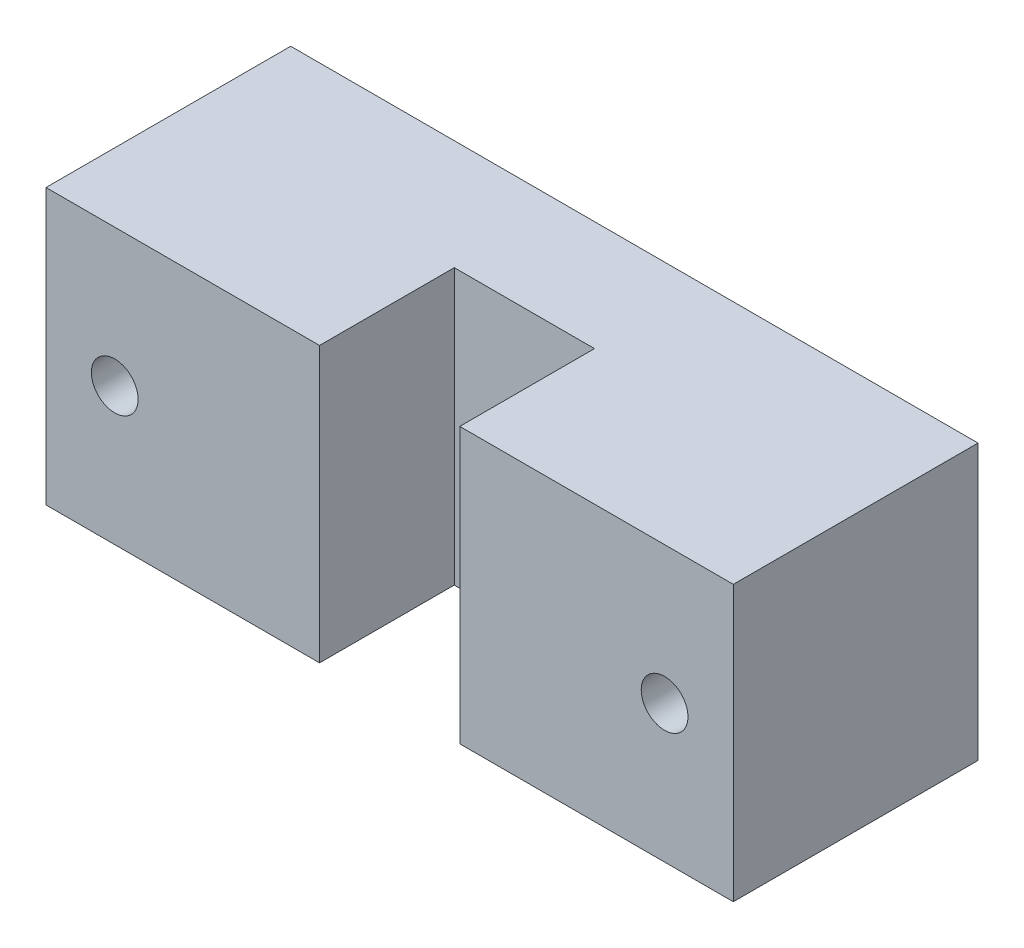
SolidWorks part; units mm, degrees
ref_plane "Спереди" through (0, 0, 0) normal (0, 0, 1) x (1, 0, 0)
ref_plane "Сверху" through (0, 0, 0) normal (0, 1, 0) x (1, 0, 0)
ref_plane "Справа" through (0, 0, 0) normal (1, 0, 0) x (0, 0, -1)
sketch "Sketch2" plane through (0, 0, 0) normal (0, 0, 1) x (1, 0, 0)
  line L0 (20, 0) -> (-20, 0) construction
  line L1 (25, -10) -> (-25, -10)
  line L2 (25, -10) -> (25, 10)
  line L3 (25, 10) -> (-25, 10)
  line L4 (-25, -10) -> (-25, 10)
  line L5 (25, -10) -> (-25, 10) construction
  line L6 (25, 10) -> (-25, -10) construction
  circle A0 centre (-20, 0) radius 1.7
  circle A1 centre (20, 0) radius 1.7
  point P0 (0, 0)
  point P9 (0, 0)
  dimension "D4" = 3.4
  dimension "D1" = 20
  dimension "D2" = 50
  dimension "D3" = 40
extrude "Boss-Extrude1" add sketch "Sketch2" along normal blind 8
sketch "Sketch5" plane through (0, -10, 0) normal (0, -1, 0) x (1, 0, 0)
  line L0 (-25, 8) -> (-25, 17.8)
  line L1 (-25, 8) -> (25, 8) construction
  line L2 (-25, 17.8) -> (-5.1, 17.8)
  line L3 (-5.1, 17.8) -> (-5.1, 8)
  line L4 (-5.1, 8) -> (5.1, 8)
  line L5 (5.1, 8) -> (5.1, 17.8)
  line L6 (5.1, 17.8) -> (25, 17.8)
  line L7 (25, 17.8) -> (25, 8)
  line L8 (25, 8) -> (-25, 8) construction
  line L9 (-25, 0) -> (25, 0) construction
  line L10 (0, 8) -> (0, 0) construction
  line L11 (-25, 8) -> (-25, 0) construction
  arc A0 (-25, 8) -> (25, 8) centre (0, 43.0625) ccw
  point P17 (0, 0)
  dimension "D1" = 10.2
  dimension "D3" = 9.8
extrude "Boss-Extrude2" add sketch "Sketch5" against normal up to surface (20 mm away) up to face at (0, 10, 4)
sketch "Sketch6" plane through (0, 0, 0) normal (0, 0, -1) x (-1, 0, 0)
  circle A0 centre (20, 0) radius 3.75
  circle A1 centre (-20, 0) radius 3.75
  dimension "D1" = 7.5
extrude "Cut-Extrude1" cut sketch "Sketch6" against normal blind 4
sketch "Sketch7" plane through (0, 0, 0) normal (0, 0, -1) x (-1, 0, 0)
  circle A0 centre (20, 0) radius 1.7
  circle A1 centre (20, 0) radius 1.7 construction
  circle A2 centre (-20, 0) radius 1.7
  circle A4 centre (-20, 0) radius 1.7 construction
extrude "Cut-Extrude2" cut sketch "Sketch7" against normal through all
